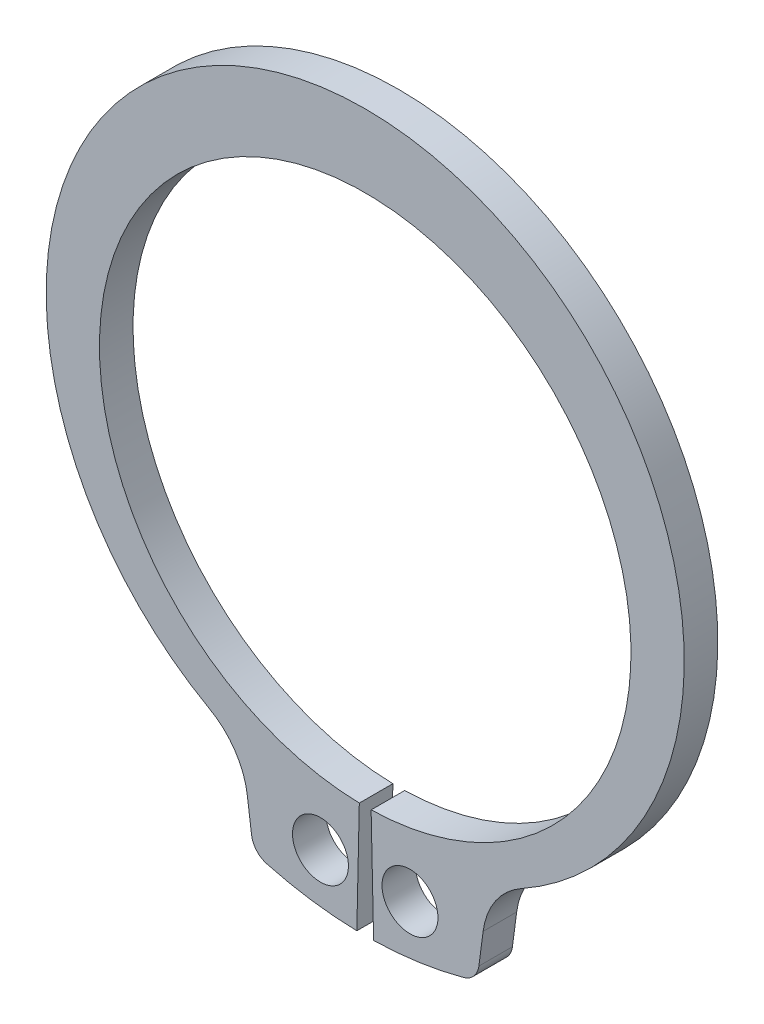
SolidWorks part; units mm, degrees
ref_plane "Plane1" through (0, 0, 0) normal (0, 0, 1) x (1, 0, 0)
ref_plane "Plane2" through (0, 0, 0) normal (0, 1, 0) x (1, 0, 0)
ref_plane "Plane3" through (0, 0, 0) normal (1, 0, 0) x (0, 0, -1)
sketch "Clipboard" plane through (0, 0, 0) normal (0, 0, 1) x (1, 0, 0)
  line L0 (0, 0) -> (2.6, 0)
  line L1 (0, 0) -> (0, 1.3)
  line L2 (0, 0) -> (0, -4)
  circle A0 centre (0, 0) radius 1
  circle A1 centre (0, 0) radius 10
  dimension "HoleDia" = 2
  dimension "ShaftDia" = 20
  dimension "LargeSection" = 2.6
  dimension "SmallSection" = 1.3
  dimension "LugSection" = 4
sketch "BodySke" plane through (0, 0, 0) normal (0, 0, 1) x (1, 0, 0)
  line L0 (-1.5431, 0) -> (1.5431, 0) construction
  line L1 (0, 0) -> (0, 12.1) construction
  line L2 (0.2111, -9.4977) -> (0.3, -13.4967)
  line L3 (-0.2111, -9.4977) -> (-0.3, -13.4967)
  line L4 (0, 0) -> (6.8901, -11.6093) construction
  line L5 (0, 0) -> (-6.8901, -11.6093) construction
  line L7 (4.2143, -11.257) -> (4.0627, -12.4083)
  line L8 (-4.2143, -11.257) -> (-4.0627, -12.4083)
  circle A0 centre (0, 0) radius 9.5 construction
  arc A1 (0.2111, -9.4977) -> (-0.2111, -9.4977) centre (0, 0) ccw
  arc A2 (5.5121, -9.2874) -> (-5.5121, -9.2874) centre (0, 0.696) ccw construction
  arc A3 (0.3, -13.4967) -> (3.5144, -13.0345) centre (0, 0) ccw
  arc A4 (5.5715, -9.2544) -> (4.2143, -11.257) centre (6.8901, -11.6093) ccw
  arc A5 (-4.2143, -11.257) -> (-5.5715, -9.2544) centre (-6.8901, -11.6093) ccw
  arc A6 (-3.5144, -13.0345) -> (-0.3, -13.4967) centre (0, 0) ccw
  arc A7 (5.5715, -9.2544) -> (-5.5715, -9.2544) centre (0, 0.696) ccw
  arc A8 (-4.2543, -10.9528) -> (4.2543, -10.9528) centre (0, 0) ccw construction
  circle A9 centre (1.6, -11.6406) radius 1
  circle A10 centre (-1.6, -11.6406) radius 1
  arc A11 (4.0627, -12.4083) -> (3.5144, -13.0345) centre (3.3191, -12.3104) cw
  arc A12 (-4.0627, -12.4083) -> (-3.5144, -13.0345) centre (-3.3191, -12.3104) ccw
  point P28 (3.9988, -12.8942)
  point P31 (-3.9988, -12.8942)
  dimension "HoleDia" = 2
  dimension "GrooveDia" = 19
  dimension "LugRad" = 13.5
  dimension "HoleOffsetRad" = 11.75
  dimension "D3" = 0.75
  dimension "LargeRad" = 12.1
  dimension "SmallRad" = 10.8
  dimension "SmallAngle" = 61.378
  dimension "D2" = 15
  dimension "HoleSpacing" = 3.2
  dimension "Gap" = 0.6
extrude "Body" add sketch "BodySke" against normal blind 1.2
sketch "NotSke" plane through (0, 0, 0) normal (0, 0, 1) x (1, 0, 0)
  line L0 (1.6, -10.6406) -> (1.6, -12.6406)
  line L1 (1.6, -12.6406) -> (-1.6, -12.6406)
  line L2 (-1.6, -12.6406) -> (-1.6, -10.6406)
  line L3 (-1.6, -10.6406) -> (1.6, -10.6406)
  circle A0 centre (1.6, -11.6406) radius 1 construction
  circle A1 centre (-1.6, -11.6406) radius 1 construction
extrude "Notch" [suppressed] cut sketch "NotSke" against normal through all
sketch "UnlSke" plane through (0, 0, 0) normal (0, 0, 1) x (1, 0, 0)
  line L0 (-2.9699, -13.1693) -> (-2.0899, -9.2673)
  line L1 (2.9699, -13.1693) -> (2.0899, -9.2673)
  arc A0 (2.0899, -9.2673) -> (-2.0899, -9.2673) centre (0, 0) ccw
  arc A1 (2.9699, -13.1693) -> (-2.9699, -13.1693) centre (0, 0) ccw
  arc A2 (0.3, -13.4967) -> (3.5144, -13.0345) centre (0, 0) ccw construction
  arc A3 (0.2111, -9.4977) -> (-0.2111, -9.4977) centre (0, 0) ccw construction
  circle A4 centre (-1.6, -11.6406) radius 1 construction
  circle A5 centre (1.6, -11.6406) radius 1 construction
extrude "Unlug" [suppressed] add sketch "UnlSke" against normal through all
equation "' \"ShaftDia@Clipboard\" = 3"
equation "' \"Thickness@Body\" = 0.4"
equation "' \"GrooveDia@BodySke\" = 2.8"
equation "' \"LugSection@Clipboard\" = 1.9"
equation "' \"LargeSection@Clipboard\" = 0.8"
equation "' \"HoleDia@Clipboard\" = 1.0"
equation "' \"ShaftDia@Clipboard\" = 10"
equation "' \"Thickness@Body\" = 1.0"
equation "' \"GrooveDia@BodySke\" = 9.6"
equation "' \"LugSection@Clipboard\" = 3.3"
equation "' \"LargeSection@Clipboard\" = 1.8"
equation "' \"HoleDia@Clipboard\" = 1.5"
equation "\"SmallSection@Clipboard\" = \"LargeSection@Clipboard\" * 0.5"
equation "\"Gap@BodySke\" =  \"Thickness@Body\" / 2"
equation "\"LargeRad@BodySke\" =  \"GrooveDia@BodySke\" / 2 +  \"LargeSection@Clipboard\""
equation "\"SmallRad@BodySke\" =  \"GrooveDia@BodySke\" / 2 +  \"SmallSection@Clipboard\""
equation "\"LugRad@BodySke\" = \"GrooveDia@BodySke\" / 2 + \"LugSection@Clipboard\""
equation "\"HoleOffsetRad@BodySke\" = (  \"ShaftDia@Clipboard\" / 2 + \"LugRad@BodySke\" ) / 2"
equation "\"HoleSpacing@BodySke\" = \"Gap@BodySke\"  * 2 +  \"HoleDia@Clipboard\""
equation "\"HoleDia@BodySke\" =  \"HoleDia@Clipboard\""
equation "\"SmallAngle@BodySke\" = atn(\"HoleSpacing@BodySke\" / 2 / sqr(\"HoleOffsetRad@BodySke\"  * \"HoleOffsetRad@BodySke\" - (\"HoleSpacing@BodySke\" / 2) * (\"HoleSpacing@BodySke\" / 2) ))  * 7 *  (\"LargeRad@BodySke\" / \"SmallRad@BodySke\")* ( 180 / 3.141593)"
